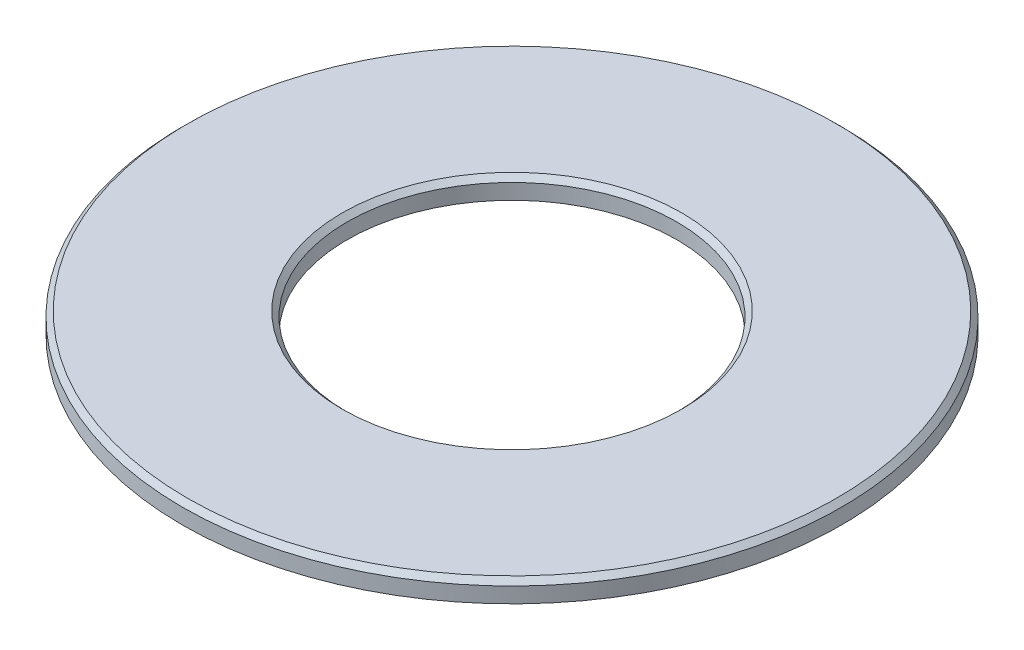
SolidWorks part; units mm, degrees
ref_plane "Ebene vorne" through (0, 0, 0) normal (0, 0, 1) x (1, 0, 0)
ref_plane "Ebene oben" through (0, 0, 0) normal (0, 1, 0) x (1, 0, 0)
ref_plane "Ebene rechts" through (0, 0, 0) normal (1, 0, 0) x (0, 0, -1)
sketch "Skizze1" plane through (0, 0, 0) normal (0, 0, 1) x (1, 0, 0)
  line L0 (0, 0) -> (0, 1.6555) construction
  line L1 (1.6, 0.2) -> (1.6, 0)
  line L2 (1.6, 0) -> (3.2, 0)
  line L3 (3.2, 0) -> (3.2, 0.2)
  line L4 (3.2, 0.2) -> (1.6, 0.2)
  dimension "D1" = 3.2
  dimension "D2" = 6.4
  dimension "D3" = 0.2
revolve "Rotation1" add sketch "Skizze1" angle 360 about L0
chamfer "Fase1" distance 0.05 angle 45 2 edges at (0, 0.2, -3.2) (0, 0.2, -1.6)
